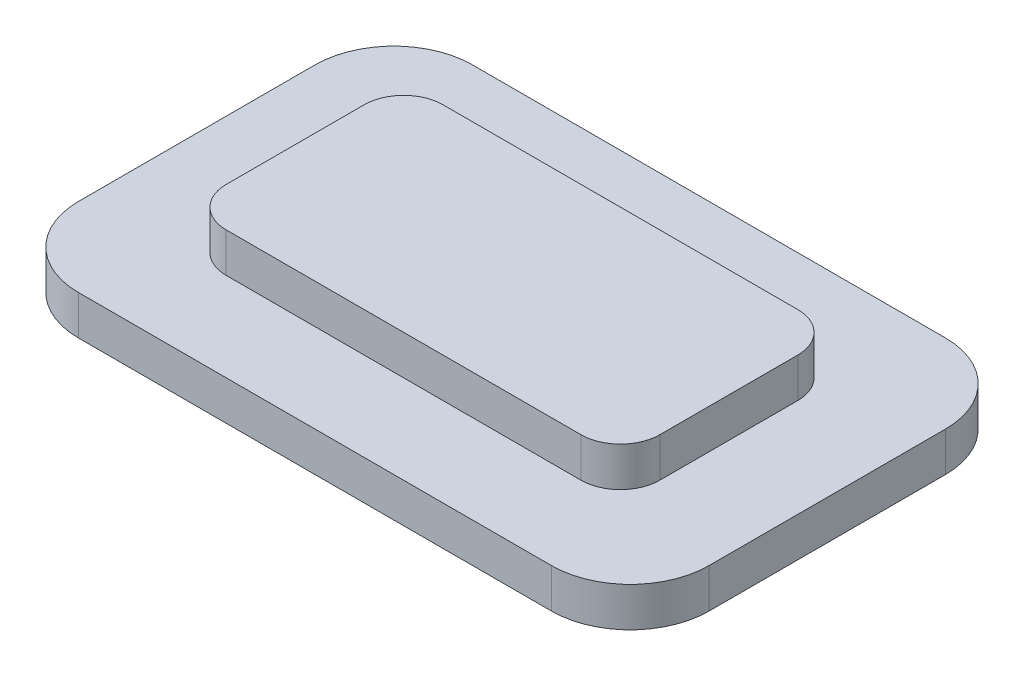
SolidWorks part; units mm, degrees
ref_plane "Front Plane" through (0, 0, 0) normal (0, 0, 1) x (1, 0, 0)
ref_plane "Top Plane" through (0, 0, 0) normal (0, 1, 0) x (1, 0, 0)
ref_plane "Right Plane" through (0, 0, 0) normal (1, 0, 0) x (0, 0, -1)
other "Configuration Table"
sketch "Sketch1" plane through (0, 0, 0) normal (0, 1, 0) x (1, 0, 0)
  line L1 (5.5, 2.75) -> (-5.5, 2.75)
  line L2 (5.5, 2.75) -> (5.5, -2.75)
  line L3 (5.5, -2.75) -> (-5.5, -2.75)
  line L4 (-5.5, 2.75) -> (-5.5, -2.75)
  line L5 (5.5, 2.75) -> (-5.5, -2.75) construction
  line L6 (5.5, -2.75) -> (-5.5, 2.75) construction
  point P0 (0, 0)
  dimension "D1" = 5.5
  dimension "D2" = 11
extrude "Boss-Extrude1" add sketch "Sketch1" along normal blind 1 contours L2 L1 L4 L3
sketch "Sketch2" plane through (0, 0, 0) normal (0, -1, 0) x (1, 0, 0)
  line L1 (6, 5) -> (-6, 5)
  line L2 (8, 3) -> (8, -3)
  line L3 (6, -5) -> (-6, -5)
  line L4 (-8, 3) -> (-8, -3)
  line L5 (8, 5) -> (-8, -5) construction
  line L6 (8, -5) -> (-8, 5) construction
  arc A0 (6, 5) -> (8, 3) centre (6, 3) cw
  arc A1 (8, -3) -> (6, -5) centre (6, -3) cw
  arc A2 (-6, -5) -> (-8, -3) centre (-6, -3) cw
  arc A3 (-6, 5) -> (-8, 3) centre (-6, 3) ccw
  point P0 (0, 0)
  dimension "D3" = 2
  dimension "D1" = 10
  dimension "D2" = 16
extrude "Boss-Extrude2" add sketch "Sketch2" along normal blind 1
fillet "Fillet1" radius 1 4 edges at (5.5, 0.5, -2.75) (5.5, 0.5, 2.75) (-5.5, 0.5, -2.75) (-5.5, 0.5, 2.75)
